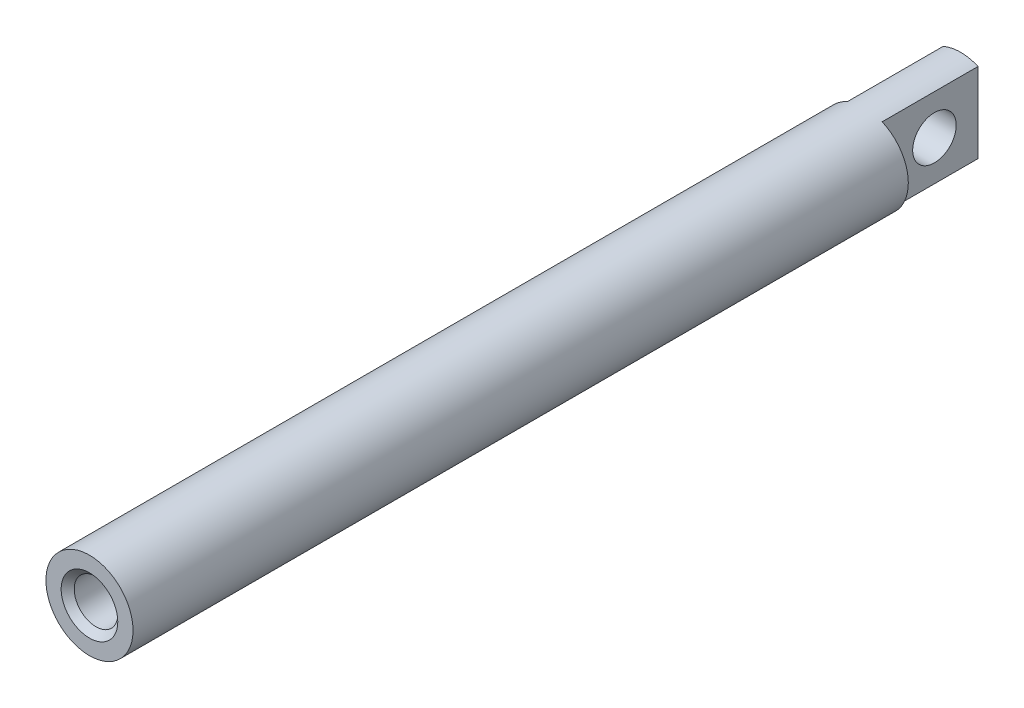
SolidWorks part; units mm, degrees
material "Plain Carbon Steel"
ref_plane "Front Plane" through (0, 0, 0) normal (0, 0, 1) x (1, 0, 0)
ref_plane "Top Plane" through (0, 0, 0) normal (0, 1, 0) x (1, 0, 0)
ref_plane "Right Plane" through (0, 0, 0) normal (1, 0, 0) x (0, 0, -1)
sketch "Sketch1" plane through (0, 0, 0) normal (0, 0, 1) x (1, 0, 0)
  circle A0 centre (0, 0) radius 5
  dimension "D1" = 10
extrude "Boss-Extrude1" add sketch "Sketch1" against normal blind 100
sketch "Sketch2" plane through (0, 0, 0) normal (0, 1, 0) x (1, 0, 0)
  line L2 (-5, 100) -> (-2, 100)
  line L3 (-5, 100) -> (-5, 89)
  line L4 (-5, 89) -> (-2, 89)
  line L5 (-2, 100) -> (-2, 89)
  line L6 (5, 100) -> (2, 100)
  line L7 (5, 100) -> (5, 89)
  line L8 (5, 89) -> (2, 89)
  line L9 (2, 100) -> (2, 89)
  dimension "D1" = 11
  dimension "D2" = 4
extrude "Cut-Extrude5" cut sketch "Sketch2" against normal up to next and the other way up to next
sketch "Sketch3" plane through (2, 0, 0) normal (1, 0, 0) x (0, 0, -1)
  line L1 (100, 4.5826) -> (100, -4.5826) construction
  circle A0 centre (95, 0) radius 2.5
  dimension "D1" = 5
  dimension "D2" = 5
extrude "Cut-Extrude6" cut sketch "Sketch3" against normal up to next
hole_wizard "M6x1.0 Tapped Hole1" positions "Sketch4" profile "Sketch5" tap size "M6x1.0" standard "ANSI Metric"
sketch "Sketch4" plane through (0, 0, 0) normal (0, 0, 1) x (1, 0, 0)
  point P0 (0, 0)
sketch "Sketch5" plane through (0, 0, 0) normal (1, 0, 0) x (0, -1, 0)
  line L0 (0, 0) -> (0, 18.5022)
  line L1 (0, 18.5022) -> (2.5, 17)
  line L2 (2.5, 17) -> (2.5, 0.75)
  line L3 (2.5, 0.75) -> (3.25, 0)
  line L5 (3.25, 0) -> (0, 0)
  line L6 (-2.5, 0.75) -> (-3.25, 0) construction
  line L10 (0, 18.5022) -> (-2.5, 17) construction
  line L11 (0, -6.35) -> (0, 107.95) construction
  dimension "Tap Drill Dia." = 5
  dimension "Tap Drill Depth" = 17
  dimension "Near C'Sink Dia." = 6.5
  dimension "Near C'Sink Angle" = 90
  dimension "Drill Angle" = 118
cosmetic thread "Hole Thread1" parameters "D1"=12, "D2"=6
